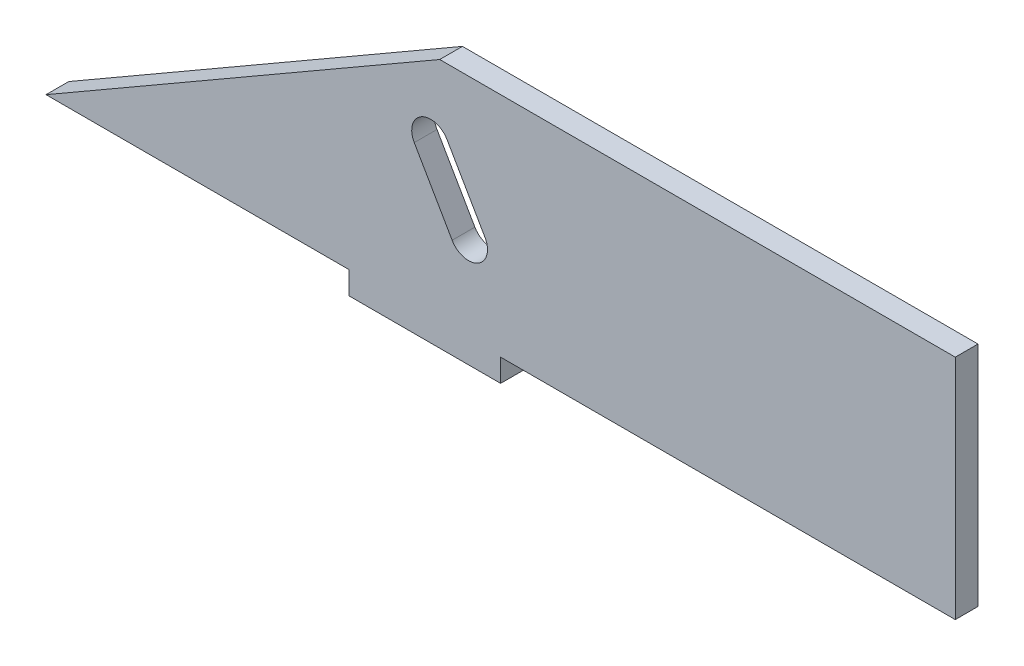
SolidWorks part; units mm, degrees
ref_plane "Front Plane" through (0, 0, 0) normal (0, 0, 1) x (1, 0, 0)
ref_plane "Top Plane" through (0, 0, 0) normal (0, 1, 0) x (1, 0, 0)
ref_plane "Right Plane" through (0, 0, 0) normal (1, 0, 0) x (0, 0, -1)
sketch "Sketch1" plane through (0, 0, 0) normal (0, 0, 1) x (1, 0, 0)
  line L0 (-10, -15) -> (-10, -18)
  line L1 (50, -15) -> (10, -15)
  line L2 (50, -15) -> (50, 15)
  line L3 (50, 15) -> (-50, 15)
  line L4 (-50, -15) -> (-50, 15)
  line L5 (50, -15) -> (-50, 15) construction
  line L6 (50, 15) -> (-50, -15) construction
  line L7 (-10, -18) -> (10, -18)
  line L8 (10, -18) -> (10, -15)
  line L9 (-10, -15) -> (-50, -15)
  point P0 (0, 0)
  dimension "D1" = 100
  dimension "D2" = 30
  dimension "D3" = 3
  dimension "D4" = 20
  dimension "D5" = 40
extrude "Boss-Extrude1" add sketch "Sketch1" along normal blind 3
sketch "Sketch4" plane through (0, 0, 3) normal (0, 0, 1) x (1, 0, 0)
  line L0 (-50, -15) -> (1.9615, 15)
  line L1 (50, 15) -> (-50, 15) construction
  line L2 (-50, 15) -> (-50, -15) construction
  line L3 (1.9615, 15) -> (-50, 15)
  line L4 (-50, 15) -> (-50, -14.2203)
  dimension "D1" = 60
extrude "Cut-Extrude3" cut sketch "Sketch4" against normal blind 3 and the other way through all
sketch "Sketch5" plane through (0, 0, 3) normal (0, 0, 1) x (1, 0, 0)
  line L0 (1.9615, 15) -> (13.7259, -5.3765) construction
  line L1 (-50, -15) -> (1.9615, 15) construction
  line L2 (-3.2346, 12) -> (8.5298, -8.3765) construction
  line L3 (7.9304, -2.3385) -> (2.9304, 6.3218)
  line L4 (3.6003, -4.8385) -> (-1.3997, 3.8218)
  arc A0 (3.6003, -4.8385) -> (7.9304, -2.3385) centre (5.7654, -3.5885) ccw
  arc A1 (2.9304, 6.3218) -> (-1.3997, 3.8218) centre (0.7654, 5.0718) ccw
  dimension "D2" = 5
  dimension "D3" = 5
  dimension "D4" = 8
  dimension "10" = 10
  dimension "D1" = 6
extrude "Cut-Extrude4" cut sketch "Sketch5" against normal blind 4
sketch "Sketch6" plane through (50, 0, 0) normal (1, 0, 0) x (0, 0, -1)
  line L0 (-3, 15) -> (0, 15) construction
  line L1 (-3, 15) -> (0, 15)
  line L2 (-3, -15) -> (-3, 15) construction
  line L3 (-3, -15) -> (-3, 15)
  line L4 (0, -15) -> (0, 15) construction
  line L5 (0, -15) -> (0, 15)
  line L6 (-3, -15) -> (0, -15) construction
  line L7 (-3, -15) -> (0, -15)
extrude "Boss-Extrude2" add sketch "Sketch6" along normal blind 20
